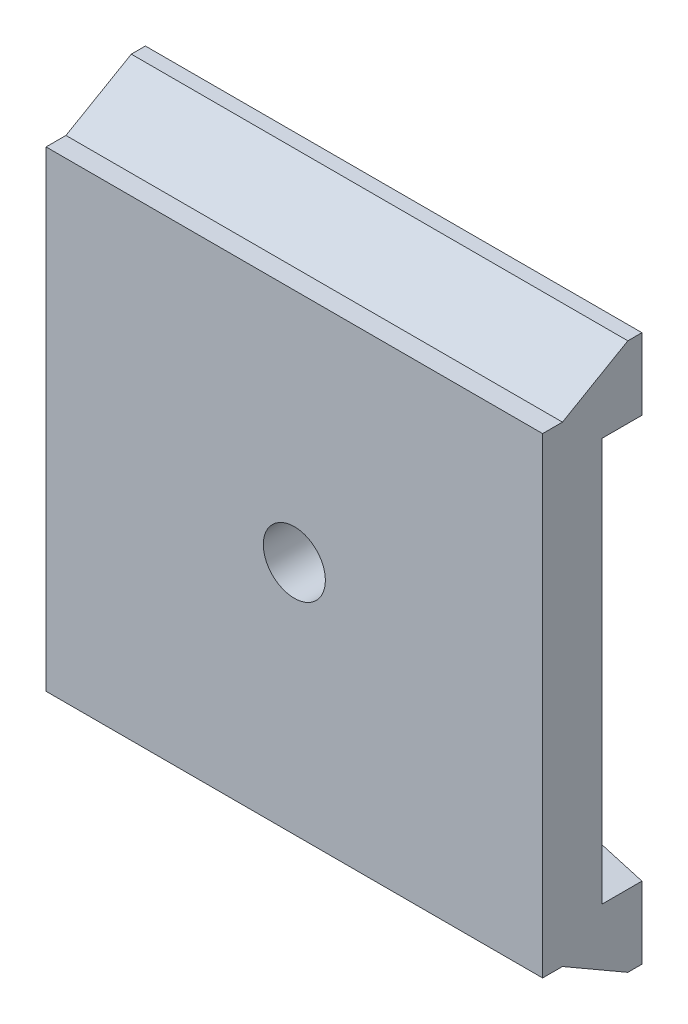
SolidWorks part; units mm, degrees
ref_plane "Front Plane" through (0, 0, 0) normal (0, 0, 1) x (1, 0, 0)
ref_plane "Top Plane" through (0, 0, 0) normal (0, 1, 0) x (1, 0, 0)
ref_plane "Right Plane" through (0, 0, 0) normal (1, 0, 0) x (0, 0, -1)
sketch "Sketch1" plane through (0, 0, 0) normal (0, 0, 1) x (1, 0, 0)
  line L1 (-25.4, 27.9781) -> (25.4, 27.9781)
  line L2 (-25.4, 27.9781) -> (-25.4, -27.9781)
  line L3 (-25.4, -27.9781) -> (25.4, -27.9781)
  line L4 (25.4, 27.9781) -> (25.4, -27.9781)
  line L5 (-25.4, 27.9781) -> (25.4, -27.9781) construction
  line L6 (-25.4, -27.9781) -> (25.4, 27.9781) construction
  point P0 (0, 0)
  dimension "D1" = 50.8
  dimension "D2" = 55.9562
extrude "Boss-Extrude1" add sketch "Sketch1" along normal blind 10.16
sketch "Sketch2" plane through (0, 0, 10.16) normal (0, 0, 1) x (1, 0, 0)
  line L0 (25.4, -27.9781) -> (25.4, 27.9781) construction
  line L1 (-25.4, 27.9781) -> (25.4, 27.9781)
  line L2 (-25.4, 27.9781) -> (-25.4, 24.1173)
  line L3 (-25.4, 24.1173) -> (25.4, 24.1173)
  line L4 (25.4, 27.9781) -> (25.4, 24.1173)
  line L6 (-25.4, -27.9781) -> (25.4, -27.9781)
  line L7 (-25.4, -27.9781) -> (-25.4, -24.1173)
  line L8 (-25.4, -24.1173) -> (25.4, -24.1173)
  line L9 (25.4, -27.9781) -> (25.4, -24.1173)
  dimension "D1" = 3.8608
  dimension "D2" = 3.8608
extrude "Cut-Extrude1" cut sketch "Sketch2" against normal blind 2.032
sketch "Sketch3" plane through (-25.4, 0, 0) normal (-1, 0, 0) x (0, 0, 1)
  line L0 (8.128, 24.1173) -> (1.4409, 27.9781)
  line L1 (8.128, 27.9781) -> (0, 27.9781) construction
  line L2 (1.4409, 27.9781) -> (8.128, 27.9781)
  line L3 (8.128, 27.9781) -> (8.128, 24.1173)
  line L4 (8.128, -24.1173) -> (1.4409, -27.9781)
  line L5 (8.128, -27.9781) -> (0, -27.9781) construction
  line L6 (1.4409, -27.9781) -> (8.128, -27.9781)
  line L7 (8.128, -27.9781) -> (8.128, -24.1173)
  dimension "D1" = 30
  dimension "D2" = 30
extrude "Cut-Extrude2" cut sketch "Sketch3" against normal through all
sketch "Sketch4" plane through (0, 0, 10.16) normal (0, 0, 1) x (1, 0, 0)
  circle A0 centre (0, 0) radius 3.175
  dimension "D1" = 6.35
extrude "Cut-Extrude3" cut sketch "Sketch4" against normal through all
sketch "Sketch5" plane through (0, 0, 0) normal (0, 0, -1) x (-1, 0, 0)
  line L0 (25.4, 27.9781) -> (25.4, -27.9781) construction
  line L1 (-25.4, -16.9926) -> (25.4, -16.9926)
  line L2 (-25.4, -16.9926) -> (-25.4, 16.9926)
  line L3 (-25.4, 16.9926) -> (25.4, 16.9926)
  line L4 (25.4, -16.9926) -> (25.4, 16.9926)
  line L5 (-25.4, -16.9926) -> (25.4, 16.9926) construction
  line L6 (-25.4, 16.9926) -> (25.4, -16.9926) construction
  point P0 (0, 0)
  dimension "D1" = 33.9852
extrude "Cut-Extrude4" cut sketch "Sketch5" against normal blind 4.064
sketch "Sketch6" plane through (0, 0, 0) normal (0, 0, -1) x (-1, 0, 0)
  line L1 (6.35, 21.0058) -> (-6.35, 21.0058)
  line L2 (9.525, 17.8308) -> (9.525, -17.8308)
  line L3 (6.35, -21.0058) -> (-6.35, -21.0058)
  line L4 (-9.525, 17.8308) -> (-9.525, -17.8308)
  line L5 (9.525, 21.0058) -> (-9.525, -21.0058) construction
  line L6 (9.525, -21.0058) -> (-9.525, 21.0058) construction
  arc A0 (6.35, 21.0058) -> (9.525, 17.8308) centre (6.35, 17.8308) cw
  arc A1 (9.525, -17.8308) -> (6.35, -21.0058) centre (6.35, -17.8308) cw
  arc A2 (-6.35, -21.0058) -> (-9.525, -17.8308) centre (-6.35, -17.8308) cw
  arc A3 (-6.35, 21.0058) -> (-9.525, 17.8308) centre (-6.35, 17.8308) ccw
  point P1 (0, 0)
  dimension "D3" = 3.175
  dimension "D1" = 42.0116
  dimension "D2" = 19.05
extrude "Cut-Extrude5" cut sketch "Sketch6" against normal blind 4.064
sketch "Sketch7" plane through (0, 0, 0) normal (0, 0, -1) x (-1, 0, 0)
  line L0 (-12.7, 16.9926) -> (-25.4, 20.6588)
  line L1 (-9.525, 16.9926) -> (-25.4, 16.9926) construction
  line L2 (-25.4, 16.9926) -> (-25.4, 27.9781) construction
  line L3 (-25.4, 20.6588) -> (-25.4, 16.9926)
  line L4 (-25.4, 16.9926) -> (-12.7, 16.9926)
  line L5 (-12.8617, -16.9926) -> (-25.4, -20.6121)
  line L6 (-25.4, -16.9926) -> (-9.525, -16.9926) construction
  line L7 (-25.4, -27.9781) -> (-25.4, -16.9926) construction
  line L8 (-25.4, -20.6121) -> (-25.4, -16.9926)
  line L9 (-25.4, -16.9926) -> (-12.8617, -16.9926)
  line L10 (12.7, -16.9926) -> (25.4, -20.6588)
  line L11 (25.4, -16.9926) -> (25.4, -27.9781) construction
  line L12 (25.4, -20.6588) -> (25.4, -16.9926)
  line L13 (25.4, -16.9926) -> (12.7, -16.9926)
  line L14 (12.7, 16.9926) -> (25.4, 20.6588)
  line L15 (25.4, 16.9926) -> (9.525, 16.9926) construction
  line L16 (25.4, 27.9781) -> (25.4, 16.9926) construction
  line L17 (25.4, 20.6588) -> (25.4, 16.9926)
  line L18 (25.4, 16.9926) -> (12.7, 16.9926)
  dimension "D1" = 7.3193
  dimension "D2" = 7.366
  dimension "D3" = 7.3193
  dimension "D4" = 7.3193
  dimension "D5" = 3.175
  dimension "D7" = 3.175
extrude "Cut-Extrude6" cut sketch "Sketch7" against normal blind 4.064
